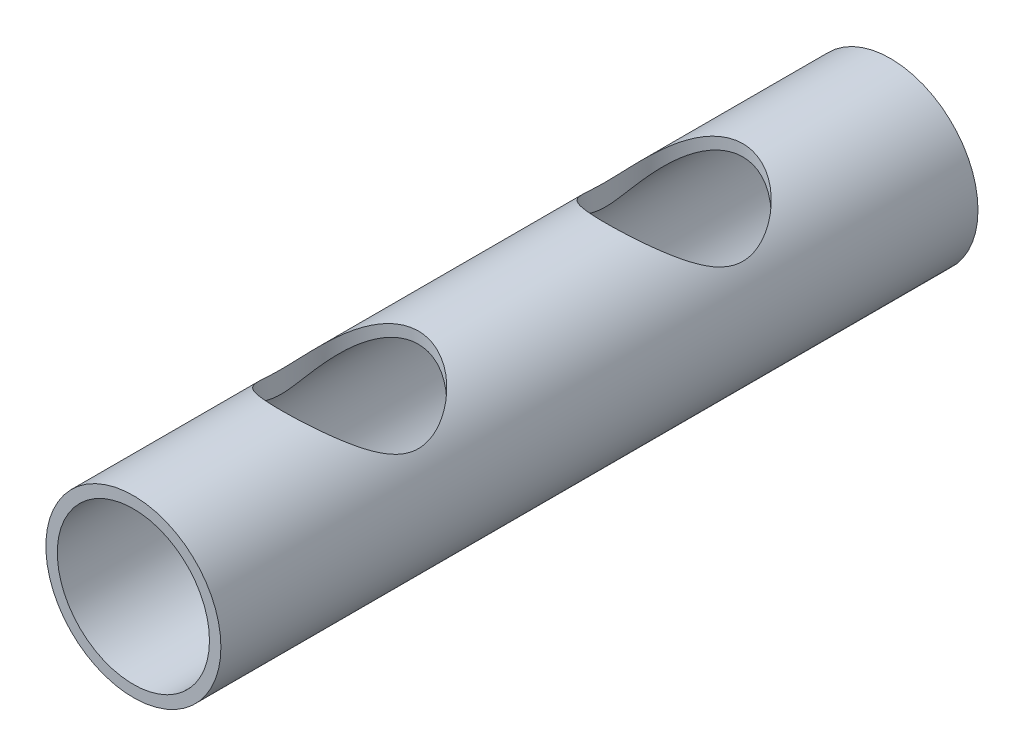
SolidWorks part; units mm, degrees
material "ABS"
ref_plane "Front Plane" through (0, 0, 0) normal (0, 0, 1) x (1, 0, 0)
ref_plane "Top Plane" through (0, 0, 0) normal (0, 1, 0) x (1, 0, 0)
ref_plane "Right Plane" through (0, 0, 0) normal (1, 0, 0) x (0, 0, -1)
sketch "Sketch1" plane through (0, 0, 0) normal (0, 0, 1) x (1, 0, 0)
  circle A0 centre (0, 0) radius 24.28
  circle A1 centre (0, 0) radius 21.105
  dimension "D1" = 48.56
  dimension "D2" = 3.175
extrude "Boss-Extrude1" add sketch "Sketch1" along normal blind 210
sketch "Sketch2" plane through (0, 0, 0) normal (0, 1, 0) x (1, 0, 0)
  line L1 (24.28, 0) -> (-24.28, 0) construction
  line L2 (-24.28, -210) -> (24.28, -210) construction
  circle A1 centre (0, -150) radius 19.05
  circle A2 centre (0, -60) radius 19.05
  dimension "D3" = 60
  dimension "D4" = 60
extrude "Cut-Extrude1" cut sketch "Sketch2" along normal blind 100
